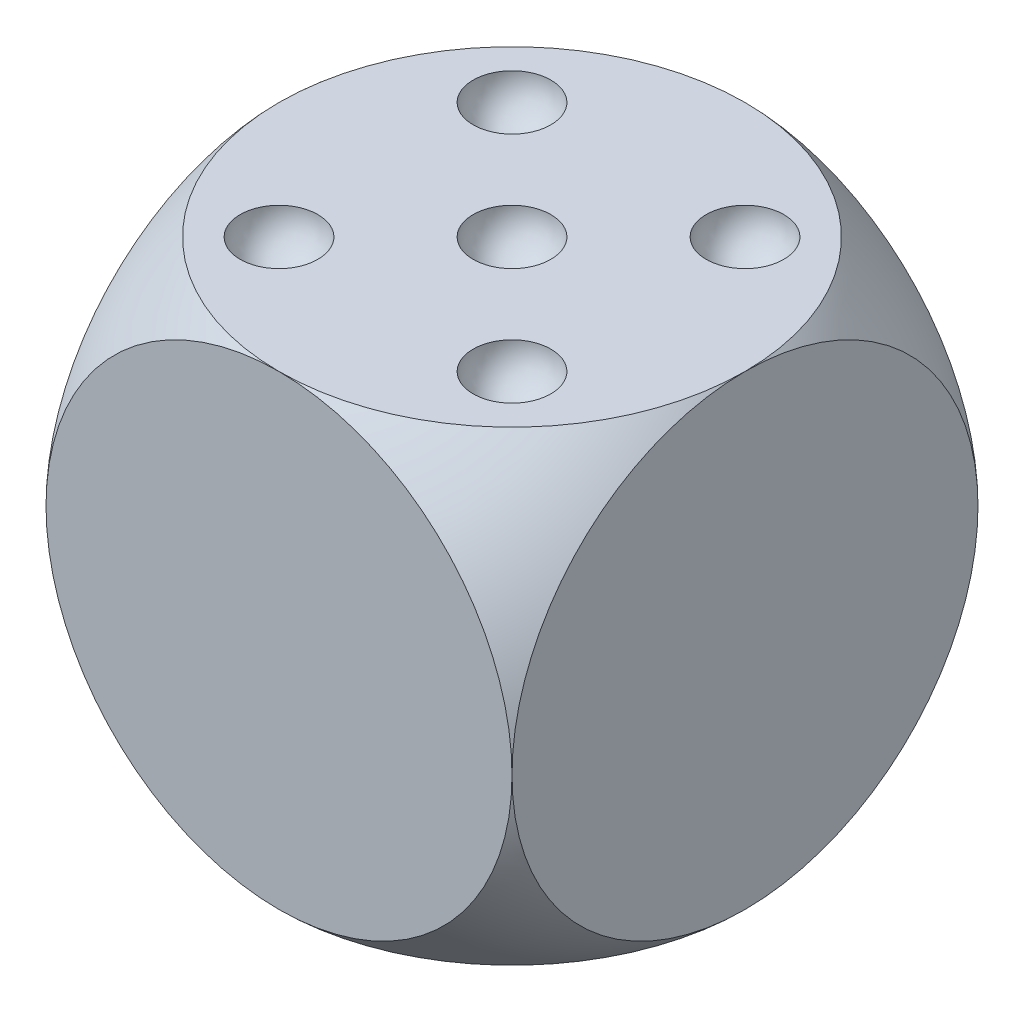
SolidWorks part; units mm, degrees
ref_plane "Front Plane" through (0, 0, 0) normal (0, 0, 1) x (1, 0, 0)
ref_plane "Top Plane" through (0, 0, 0) normal (0, 1, 0) x (1, 0, 0)
ref_plane "Right Plane" through (0, 0, 0) normal (1, 0, 0) x (0, 0, -1)
sketch "Sketch1" plane through (0, 0, 0) normal (0, 0, 1) x (1, 0, 0)
  line L0 (-106.5258, 0) -> (137.6013, 0) construction
  line L1 (0, 88.6179) -> (0, -95.9918) construction
  line L3 (-30, 30) -> (30, 30)
  line L4 (-30, 30) -> (-30, -30)
  line L5 (-30, -30) -> (30, -30)
  line L6 (30, 30) -> (30, -30)
  line L7 (-30, 30) -> (30, -30) construction
  line L8 (-30, -30) -> (30, 30) construction
  point P5 (0, 0)
  dimension "D1" = 60
  dimension "D2" = 60
extrude "Boss-Extrude1" add sketch "Sketch1" along normal mid plane 60
sketch "Sketch3" plane through (0, 0, 0) normal (0, 1, 0) x (1, 0, 0)
  line L0 (-52.9889, 0) -> (61.2176, 0) construction
  line L1 (0, 60.9126) -> (0, -91.9898) construction
  line L3 (0, -50) -> (62, -50)
  line L4 (0, -50) -> (0, -42.4264)
  line L5 (0, 50) -> (62, 50)
  line L6 (62, -50) -> (62, 50)
  line L7 (0, 42.4264) -> (0, 50)
  arc A0 (0, -42.4264) -> (0, 42.4264) centre (0, 0) ccw
  dimension "D2" = 100
  dimension "D3" = 50
revolve "Cut-Revolve1" cut sketch "Sketch3" angle 360 about L1
sketch "Sketch4" plane through (0, 30, 0) normal (0, 1, 0) x (1, 0, 0)
  line L0 (-79.6628, 0) -> (83.361, 0) construction
  line L1 (0, 47.0245) -> (0, -45.8541) construction
  line L2 (-79.6628, -15) -> (83.361, -15) construction
  line L3 (-15, 47.0245) -> (-15, -45.8541) construction
  line L4 (-30, -30) -> (0, -30) construction
  line L5 (-30, 0) -> (-30, -30) construction
  line L6 (-15, -10) -> (-15, -20)
  arc A0 (-15, -20) -> (-15, -10) centre (-15, -15) ccw
  dimension "D3" = 10
  dimension "D1" = 15
  dimension "D2" = 15
revolve "Cut-Revolve2" cut sketch "Sketch4" angle 360 about L6
pattern_linear "LPattern2" count 3 spacing 15 along (0, 0, -1) count 3 spacing 15 along (1, 0, 0) skipping (0, 1), (1, 0), (1, 2), (2, 1) of "Cut-Revolve2"
sketch "Sketch5" plane through (30, 0, 0) normal (1, 0, 0) x (0, 0, -1)
  line L0 (17.5534, -42.6231) -> (17.5534, 43.7988) construction
  line L1 (-35.9179, -22.8058) -> (46.048, -22.8058) construction
  line L2 (-30, -30) -> (0, -30) construction
  dimension "D1" = 7.1942
